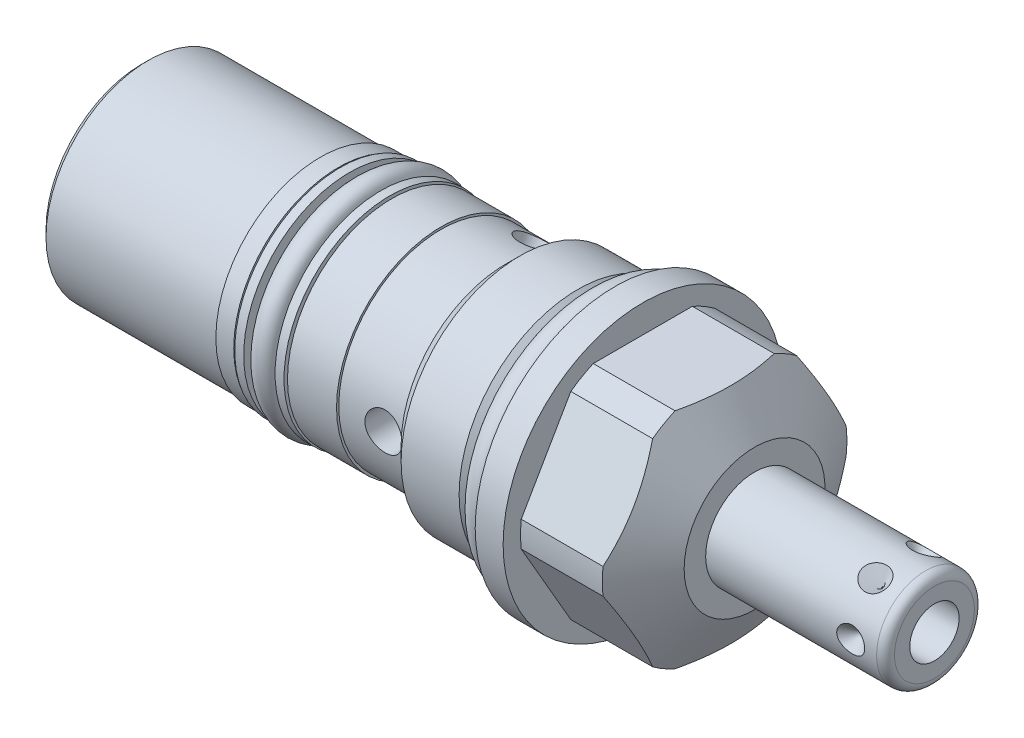
SolidWorks part; units mm, degrees
material "Alloy Steel"
ref_plane "Front Plane" through (0, 0, 0) normal (0, 0, 1) x (1, 0, 0)
ref_plane "Top Plane" through (0, 0, 0) normal (0, 1, 0) x (1, 0, 0)
ref_plane "Right Plane" through (0, 0, 0) normal (1, 0, 0) x (0, 0, -1)
sketch "Sketch1" plane through (0, 0, 0) normal (0, 0, 1) x (1, 0, 0)
  line L0 (0, 0) -> (113.8544, 0) construction
  line L1 (0, 15.875) -> (3.175, 15.875)
  line L2 (3.175, 15.875) -> (3.175, 13.8938)
  line L3 (3.175, 13.8938) -> (12.4728, 13.8938)
  line L4 (12.4728, 13.8938) -> (15.875, 8.001)
  line L5 (15.875, 8.001) -> (15.875, 0)
  line L6 (15.875, 0) -> (-53.7972, 0)
  line L7 (-53.7972, 0) -> (-53.7972, 11.6205)
  line L8 (0, 15.875) -> (0, 12.0015)
  line L9 (0, 12.0015) -> (-2.7178, 12.0015)
  line L10 (-2.7178, 12.0015) -> (-4.21, 13.4937)
  line L11 (-4.21, 13.4937) -> (-10.8013, 13.4937)
  line L12 (-10.8013, 13.4937) -> (-12.4206, 11.8745)
  line L14 (-12.4206, 11.8745) -> (-12.4206, 11.6205)
  line L15 (-12.4206, 11.6205) -> (-53.7972, 11.6205)
  dimension "D1" = 31.75
  dimension "D2" = 16.002
  dimension "D3" = 3.175
  dimension "D4" = 15.875
  dimension "D5" = 27.7876
  dimension "D6" = 30
  dimension "D7" = 53.7972
  dimension "D8" = 51.0794
  dimension "D9" = 24.003
  dimension "D10" = 45
  dimension "D11" = 26.9875
  dimension "D12" = 9.7028
  dimension "D13" = 23.749
  dimension "D14" = 23.241
revolve "Revolve1" add sketch "Sketch1" angle 360 about L0
sketch "Sketch2" plane through (15.875, 0, 0) normal (1, 0, 0) x (0, 0, -1)
  line L1 (7.3323, 12.7) -> (-7.3323, 12.7)
  line L2 (-7.3323, 12.7) -> (-14.6647, 0)
  line L3 (-14.6647, 0) -> (-7.3323, -12.7)
  line L4 (-7.3323, -12.7) -> (7.3323, -12.7)
  line L5 (7.3323, -12.7) -> (14.6647, 0)
  line L6 (14.6647, 0) -> (7.3323, 12.7)
  circle A0 centre (0, 0) radius 12.7 construction
  dimension "D1" = 25.4
extrude "Cut-Extrude1" cut sketch "Sketch2" against normal up to surface (12.7 mm away) flip side to cut up to face at (3.175, 0, 15.875)
sketch "Sketch3" plane through (0, 0, 0) normal (0, 0, 1) x (1, 0, 0)
  line L0 (0, 0) -> (52.5154, 0) construction
  line L1 (15.875, 5.5563) -> (35.306, 5.5562)
  line L2 (15.875, -8.001) -> (15.875, 8.001) construction
  line L3 (36.322, 4.5402) -> (36.322, 0)
  line L4 (36.322, 0) -> (15.875, 0)
  line L5 (15.875, 0) -> (15.875, 5.5563)
  line L6 (0, 15.875) -> (0, -15.875) construction
  arc A0 (36.322, 4.5402) -> (35.306, 5.5562) centre (35.306, 4.5402) ccw
  dimension "D1" = 1.016
  dimension "D2" = 36.322
  dimension "D3" = 11.1125
revolve "Revolve2" add sketch "Sketch3" angle 360 about L0
sketch "Sketch4" plane through (0, 0, 0) normal (0, 1, 0) x (1, 0, 0)
  line L0 (32.3596, 10.0738) -> (32.3596, 0) construction
  line L1 (36.322, -4.5402) -> (36.322, 4.5402) construction
  line L2 (33.9471, 5.5563) -> (32.3596, 5.5563)
  line L3 (35.306, 5.5563) -> (15.875, 5.5563) construction
  line L4 (32.3596, 5.5563) -> (32.3596, 3.9687)
  line L5 (32.3596, 3.9687) -> (33.9471, 5.5563)
  dimension "D1" = 3.9624
  dimension "D2" = 45
  dimension "D3" = 3.175
revolve "Cut-Revolve1" cut sketch "Sketch4" angle 360 about L0
pattern_circular "CirPattern1" count 6 over 360 about axis through (0, 0, 0) along (-1, 0, 0) of "Cut-Revolve1"
sketch "Sketch5" plane through (0, 0, 0) normal (0, 0, 1) x (1, 0, 0)
  line L0 (0, 0) -> (44.9273, 0) construction
  line L1 (36.322, 2.8067) -> (26.162, 2.8067)
  line L2 (36.322, -4.5402) -> (36.322, 4.5402) construction
  line L3 (26.162, 2.8067) -> (24.4756, 0)
  line L4 (24.4756, 0) -> (36.322, 0)
  line L5 (36.322, 0) -> (36.322, 2.8067)
  dimension "D1" = 10.16
  dimension "D2" = 59
  dimension "D3" = 5.6134
revolve "Cut-Revolve2" cut sketch "Sketch5" angle 360 about L0
sketch "Sketch6" plane through (0, 0, 0) normal (0, 0, 1) x (1, 0, 0)
  line L0 (-19.7612, 11.6205) -> (-19.7612, 11.8745)
  line L1 (-12.4206, 11.6205) -> (-53.7972, 11.6205) construction
  line L2 (-19.7612, 11.8745) -> (-33.4772, 11.8745)
  line L3 (-33.4772, 11.8745) -> (-33.4772, 11.6205)
  line L4 (-33.4772, 11.6205) -> (-19.7612, 11.6205)
  line L5 (0, 0) -> (-62.9111, 0) construction
  line L6 (-53.7972, 11.6205) -> (-53.7972, -11.6205) construction
  dimension "D1" = 13.716
  dimension "D2" = 23.749
  dimension "D3" = 20.32
revolve "Revolve3" add sketch "Sketch6" angle 360 about L5
sketch "Sketch7" plane through (-53.7972, 0, 0) normal (-1, 0, 0) x (0, 0, 1)
  circle A0 centre (0, 0) radius 0.8001
  dimension "D1" = 1.6002
extrude "Cut-Extrude2" cut sketch "Sketch7" against normal blind 0.762
sketch "Sketch8" plane through (0, 0, 0) normal (0, 0, 1) x (1, 0, 0)
  line L0 (0, 0) -> (-56.7277, 0) construction
  line L1 (-19.7612, 11.8745) -> (-33.4772, 11.8745) construction
  line L2 (-31.4452, 11.8745) -> (-25.3365, 11.8745)
  line L3 (-31.4452, 11.8745) -> (-31.4452, 9.8298)
  line L4 (-31.4452, 9.8298) -> (-25.3365, 9.8298)
  line L5 (-25.3365, 11.8745) -> (-25.3365, 9.8298)
  line L6 (-53.7972, 11.6205) -> (-53.7972, -11.6205) construction
  dimension "D1" = 6.1087
  dimension "D2" = 22.352
  dimension "D3" = 19.6596
revolve "Cut-Revolve3" cut sketch "Sketch8" angle 360 about L0
sketch "Sketch9" plane through (0, 0, 0) normal (0, 0, 1) x (1, 0, 0)
  line L0 (0, 0) -> (-59.2046, 0) construction
  line L1 (-28.3908, 14.9069) -> (-28.3908, -14.8344) construction
  line L2 (-31.4452, -11.8745) -> (-31.4452, 11.8745) construction
  line L3 (-25.3365, 9.8298) -> (-25.3365, -9.8298) construction
  line L4 (-25.3365, 9.8298) -> (-31.4452, 9.8298) construction
  line L5 (-26.6065, 12.0142) -> (-25.5905, 12.0142)
  line L6 (-26.6065, 12.0142) -> (-26.6065, 9.8298)
  line L7 (-26.6065, 9.8298) -> (-25.5905, 9.8298)
  line L8 (-25.5905, 12.0142) -> (-25.5905, 9.8298)
  line L9 (-25.3365, 11.8745) -> (-25.3365, -11.8745) construction
  line L10 (-31.1912, 12.0142) -> (-31.1912, 9.8298)
  line L11 (-30.1752, 9.8298) -> (-31.1912, 9.8298)
  line L12 (-30.1752, 12.0142) -> (-30.1752, 9.8298)
  line L13 (-30.1752, 12.0142) -> (-31.1912, 12.0142)
  dimension "D1" = 1.016
  dimension "D2" = 0.254
  dimension "D3" = 2.1844
revolve "Revolve4" add sketch "Sketch9" angle 360 about L0
sketch "Sketch10" plane through (0, 0, 0) normal (0, 1, 0) x (1, 0, 0)
  line L0 (-14.6812, 23.0369) -> (-14.6812, -3.4735) construction
  line L1 (-53.7972, 11.6205) -> (-53.7972, -11.6205) construction
  line L2 (-14.6812, -11.6205) -> (-16.7894, -11.6205)
  line L4 (-16.7894, -11.6205) -> (-16.7894, -0.7937)
  line L5 (-16.7894, -0.7937) -> (-14.6812, -0.7937)
  line L6 (-14.6812, -0.7937) -> (-14.6812, -11.6205)
  line L7 (-19.7612, -11.6205) -> (-12.4206, -11.6205) construction
  dimension "D1" = 39.116
  dimension "D2" = 4.2164
  dimension "D3" = 0.7937
revolve "Cut-Revolve4" cut sketch "Sketch10" angle 360 about L0
pattern_circular "CirPattern2" count 3 over 360 about axis through (0, 0, 0) along (1, 0, 0) of "Cut-Revolve4"
chamfer "Chamfer1" distance 0.762 angle 45 1 edges at (-53.7972, 0, 11.6205)
sketch "Sketch11" plane through (0, 0, 0) normal (0, 0, 1) x (1, 0, 0)
  line L0 (0, 0) -> (23.6366, 0) construction
  line L1 (0, 15.875) -> (0, -15.875) construction
  line L2 (0, 12.0015) -> (-2.7178, 12.0015) construction
  circle A0 centre (-1.4732, 13.4747) radius 1.4732
  dimension "D1" = 2.9464
  dimension "D2" = 26.9494
revolve "Revolve5" add sketch "Sketch11" angle 360 about L0
sketch "Sketch12" plane through (0, 0, 0) normal (0, 0, 1) x (1, 0, 0)
  line L0 (0, 0) -> (-56.0967, 0) construction
  line L1 (-26.6065, 9.8298) -> (-30.1752, 9.8298) construction
  line L2 (-28.3908, 11.1379) -> (-28.3908, 6.0377) construction
  line L3 (-31.4452, -11.8745) -> (-31.4452, 11.8745) construction
  line L4 (-25.3365, 9.8298) -> (-25.3365, -9.8298) construction
  circle A0 centre (-28.3908, 11.1379) radius 1.3081
  dimension "D1" = 2.6162
revolve "Revolve7" add sketch "Sketch12" angle 360 about L0
sketch "Sketch13" plane through (0, 0, 0) normal (0, 0, 1) x (1, 0, 0)
  line L0 (-63.2754, 0) -> (0, 0) construction
  line L1 (-53.7972, 4.572) -> (-51.7144, 4.1293)
  line L2 (-53.7972, 10.8585) -> (-53.7972, -10.8585) construction
  line L3 (-51.7144, 4.1293) -> (-51.0395, 3.4544)
  line L4 (-51.0395, 3.4544) -> (-42.0116, 3.4544)
  line L5 (-42.0116, 3.4544) -> (-42.0116, 0)
  line L6 (-42.0116, 0) -> (-53.7972, 0)
  line L7 (-53.7972, 0) -> (-53.7972, 4.572)
  dimension "D1" = 12
  dimension "D2" = 9.144
  dimension "D3" = 45
  dimension "D4" = 2.0828
  dimension "D5" = 6.9088
  dimension "D6" = 11.7856
revolve "Cut-Revolve5" cut sketch "Sketch13" angle 360 about L0
